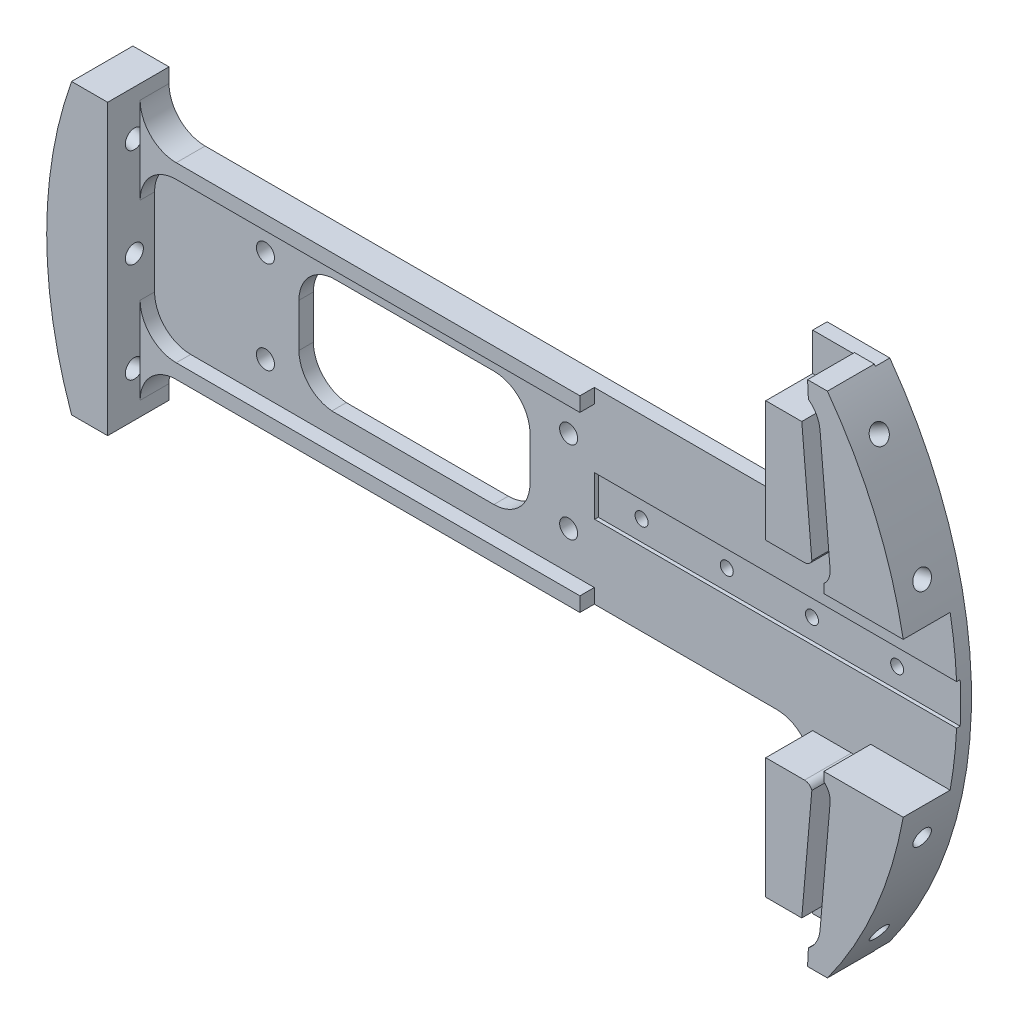
SolidWorks part; units mm, degrees
ref_plane "Front Plane" through (0, 0, 0) normal (0, 0, 1) x (1, 0, 0)
ref_plane "Top Plane" through (0, 0, 0) normal (0, 1, 0) x (1, 0, 0)
ref_plane "Right Plane" through (0, 0, 0) normal (1, 0, 0) x (0, 0, -1)
sketch "Sketch1" plane through (0, 0, 0) normal (0, 0, 1) x (1, 0, 0)
  line L0 (0, 0) -> (91.8237, 0) construction
  line L2 (-71.5726, 25.4) -> (-65.2226, 25.4)
  line L3 (50.546, 44.45) -> (50.546, 22.86)
  line L4 (50.546, -44.45) -> (50.546, -22.86)
  line L5 (44.196, -16.51) -> (-58.8726, -16.51)
  line L6 (50.546, 44.45) -> (61.5792, 44.45)
  line L7 (50.546, -44.45) -> (61.5792, -44.45)
  line L8 (-65.2226, -22.86) -> (-65.2226, -25.4)
  line L9 (44.196, 16.51) -> (-58.8726, 16.51)
  line L10 (-65.2226, 22.86) -> (-65.2226, 25.4)
  line L11 (-71.5726, -25.4) -> (-65.2226, -25.4)
  arc A0 (61.5792, -44.45) -> (61.5792, 44.45) centre (0, 0) ccw
  circle A1 centre (0, 0) radius 75.946 construction
  arc A2 (-71.5726, 25.4) -> (-71.5726, -25.4) centre (0, 0) ccw
  circle A3 centre (-45.72, 8.128) radius 1.5875
  circle A4 centre (-45.72, -8.128) radius 1.5875
  arc A5 (50.546, 22.86) -> (44.196, 16.51) centre (44.196, 22.86) cw
  arc A6 (-58.8726, 16.51) -> (-65.2226, 22.86) centre (-58.8726, 22.86) cw
  arc A7 (50.546, -22.86) -> (44.196, -16.51) centre (44.196, -22.86) ccw
  arc A8 (-58.8726, -16.51) -> (-65.2226, -22.86) centre (-58.8726, -22.86) ccw
  point P6 (75.946, 0)
  point P17 (0, 0)
  point P30 (50.546, -16.51)
  point P33 (-65.2226, -16.51)
  dimension "D1" = 75.946
  dimension "D8" = 151.892
  dimension "D11" = 75.946
  dimension "D13" = 6.35
  dimension "D7" = 3.175
  dimension ".125" = 3.175
  dimension "D2" = 27.94
  dimension "D3" = 6.35
  dimension "D4" = 11.0332
  dimension "D5" = 50.8
  dimension "D6" = 88.9
  dimension "D9" = 8.382
  dimension "D10" = 8.382
  dimension "D14" = 45.72
  dimension "1.8" = 45.72
extrude "Boss-Extrude1" add sketch "Sketch1" along normal blind 2.54
sketch "Sketch2" plane through (0, 0, 2.54) normal (0, 0, 1) x (1, 0, 0)
  line L0 (60.2463, 17.78) -> (56.2059, 64.1603) construction
  line L1 (-13.9228, 0) -> (116.9939, 0) construction
  line L2 (35.7924, 17.78) -> (109.7023, 17.78) construction
  line L3 (61.8653, 17.78) -> (60.0951, 38.1)
  line L4 (58.6516, 17.5) -> (56.8815, 37.82)
  line L5 (56.8815, 37.82) -> (50.546, 37.82)
  line L6 (58.0471, 41.7789) -> (57.9008, 44.704)
  line L7 (57.9008, 44.704) -> (61.395, 44.704)
  line L8 (50.546, 37.82) -> (50.546, 16.5667)
  line L9 (50.546, 16.5667) -> (57.3661, 16.5667)
  line L10 (60.7595, 15.0941) -> (60.7595, 13.5449)
  line L11 (60.7595, 13.5449) -> (74.7284, 13.5449)
  line L12 (60.2463, -17.78) -> (56.2059, -64.1603) construction
  line L13 (60.7595, -13.5449) -> (74.7284, -13.5449)
  line L14 (60.7595, -15.0941) -> (60.7595, -13.5449)
  line L15 (50.546, -16.5667) -> (57.3661, -16.5667)
  line L16 (50.546, -37.82) -> (50.546, -16.5667)
  line L17 (57.9008, -44.704) -> (61.395, -44.704)
  line L18 (58.0471, -41.7789) -> (57.9008, -44.704)
  line L19 (56.8815, -37.82) -> (50.546, -37.82)
  line L20 (58.6516, -17.5) -> (56.8815, -37.82)
  line L21 (61.8653, -17.78) -> (60.0951, -38.1)
  line L22 (96.3863, 0) -> (96.3863, 82.276) construction
  arc A0 (61.5792, -44.45) -> (61.5792, 44.45) centre (0, 0) ccw construction
  arc A1 (60.0951, 38.1) -> (58.0471, 41.7789) centre (54.9639, 37.653) ccw
  arc A2 (57.3661, 16.5667) -> (58.6516, 17.5) centre (57.3661, 17.9187) ccw
  arc A3 (61.8653, 17.78) -> (60.7595, 15.0941) centre (58.7167, 17.5057) cw
  arc A4 (74.7284, 13.5449) -> (61.395, 44.704) centre (0, 0) ccw
  arc A5 (74.7284, -13.5449) -> (61.395, -44.704) centre (0, 0) cw
  arc A6 (61.8653, -17.78) -> (60.7595, -15.0941) centre (58.7167, -17.5057) ccw
  arc A7 (57.3661, -16.5667) -> (58.6516, -17.5) centre (57.3661, -17.9187) cw
  arc A8 (60.0951, -38.1) -> (58.0471, -41.7789) centre (54.9639, -37.653) cw
  point P0 (75.946, 0)
  point P1 (60.2463, 17.78)
  point P49 (96.3863, 44.704)
  dimension "D6" = 75.946
  dimension "D1" = 17.78
  dimension "D2" = 15.6997
  dimension "D3" = 85.021
  dimension "D4" = 1.6129
  dimension "D5" = 20.32
  dimension "D7" = 44.704
  dimension "D8" = 44.704
  dimension "D9" = 25.4
extrude "Boss-Extrude2" add sketch "Sketch2" along normal blind 8.255
sketch "Sketch3" plane through (0, 0, 2.54) normal (0, 0, 1) x (1, 0, 0)
  line L0 (-6.3906, 0) -> (92.2963, 0) construction
  line L1 (50.546, 44.45) -> (50.546, 22.86) construction
  line L2 (12.192, -3.55) -> (76.962, -3.55)
  line L3 (12.192, -3.55) -> (12.192, 3.55)
  line L4 (12.192, 3.55) -> (76.962, 3.55)
  line L5 (76.962, -3.55) -> (76.962, 3.55)
  line L6 (12.192, -3.55) -> (76.962, 3.55) construction
  line L7 (12.192, 3.55) -> (76.962, -3.55) construction
  point P3 (44.577, 0)
  dimension "D1" = 7.1
  dimension "D2" = 64.77
  dimension "D3" = 38.354
extrude "Cut-Extrude1" cut sketch "Sketch3" against normal blind 0.635
sketch "Sketch6" plane through (0, 0, 0) normal (0, 0, -1) x (-1, 0, 0)
  line L1 (102.4877, 0) -> (-122.8054, 0) construction
sketch "Sketch7" plane through (0, 0, 0) normal (0, 0, 1) x (1, 0, 0)
  line L0 (0, 0) -> (107.1474, 0) construction
  line L1 (0, 0) -> (65.9911, 38.1) construction
  dimension "D1" = 30
ref_plane "Plane2" through (65.7712, 37.973, 0) normal (0.866, 0.5, 0) x (0, 0, -1)
sketch "Sketch9" plane through (0, 0, 2.54) normal (0, 0, 1) x (1, 0, 0)
  line L0 (-35.0108, 0) -> (91.9546, 0) construction
  circle A0 centre (7.62, -7.239) radius 1.5875
  circle A1 centre (-45.72, 8.128) radius 1.5875 construction
  circle A4 centre (7.62, 7.239) radius 1.5875
  point P9 (74.93, 0)
  dimension "D6" = 3.175
  dimension "D1" = 53.34
  dimension "D4" = 74.93
  dimension "D7" = 7.239
extrude "Cut-Extrude4" cut sketch "Sketch9" against normal through all
sketch "Sketch4" plane through (0, 0, 1.905) normal (0, 0, 1) x (1, 0, 0)
  line L0 (12.192, 3.55) -> (12.192, -3.55) construction
  line L1 (-1.4827, 0) -> (103.4049, 0) construction
  circle A0 centre (19.812, 0) radius 1.143
  circle A1 centre (34.798, 0) radius 1.143
  circle A2 centre (49.784, 0) radius 1.143
  circle A3 centre (64.77, 0) radius 1.143
  point P2 (12.192, 0)
  dimension "D2" = 2.286
  dimension "D4" = 14.986
  dimension "D1" = 7.62
  dimension "D5" = 19.812
  dimension "D3" = 4
extrude "Cut-Extrude2" cut sketch "Sketch4" against normal blind 11.43
sketch "Sketch19" plane through (0, 0, 2.54) normal (0, 0, 1) x (1, 0, 0)
  line L0 (-71.5726, -25.4) -> (-65.2226, -25.4) construction
  line L3 (-71.5726, -25.4) -> (-65.2226, -25.4)
  line L4 (-65.2226, -25.4) -> (-65.2226, 25.4)
  line L5 (-65.2226, 25.4) -> (-71.5726, 25.4) construction
  line L6 (-65.2226, 25.4) -> (-71.5726, 25.4)
  circle A0 centre (0, 0) radius 75.946 construction
  arc A3 (-71.5726, 25.4) -> (-71.5726, -25.4) centre (0, 0) ccw
  point P0 (-65.2226, -25.4)
  point P6 (-71.5726, -25.4)
  dimension "D2" = 151.892
  dimension "D1" = 6.35
extrude "Boss-Extrude5" add sketch "Sketch19" along normal blind 8.255
ref_plane "Plane3" through (0, 0, 10.795) normal (0, 0, 1) x (1, 0, 0)
sketch "Sketch22" plane through (0, 0, 10.795) normal (0, 0, 1) x (1, 0, 0)
  line L1 (-75.946, -44.45) -> (75.946, -44.45) construction
  line L2 (-75.946, -44.45) -> (-75.946, 44.45) construction
  line L3 (-75.946, 44.45) -> (75.946, 44.45) construction
  line L4 (75.946, -44.45) -> (75.946, 44.45) construction
  line L5 (-75.946, -44.45) -> (75.946, 44.45) construction
  line L6 (-75.946, 44.45) -> (75.946, -44.45) construction
  point P0 (0, 0)
  dimension "D1" = 88.9
  dimension "D2" = 151.892
sketch "Sketch24" plane through (65.7712, 37.973, 0) normal (0.866, 0.5, 0) x (0, 0, -1)
  line L0 (0, -69.2844) -> (0, 7.7053) construction
  circle A0 centre (-6.0325, -2.2244) radius 1.6383
  dimension "D1" = 3.2766
  dimension "D2" = 6.0325
sketch "Sketch25" plane through (0, 0, 0) normal (0, 0, 1) x (1, 0, 0)
  line L0 (0, 0) -> (145.0129, 0) construction
  line L1 (0, 0) -> (140.0717, -37.5321) construction
  line L2 (0, 0) -> (125.5848, -72.5064) construction
  circle A0 centre (0, 0) radius 76.2 construction
  point P9 (0, 0)
  dimension "D1" = 152.4
  dimension "D2" = 3
ref_plane "Plane4" through (0, 0, 6.096) normal (0, 0, 1) x (1, 0, 0)
sketch "Sketch27" plane through (0, 0, 6.096) normal (0, 0, 1) x (1, 0, 0)
  line L0 (-98.5098, 0) -> (76.2, 0) construction
  line L1 (0, 0) -> (143.2275, -38.3777) construction
  line L2 (0, 0) -> (128.4143, -74.14) construction
  line L3 (0, 0) -> (143.2275, 38.3777) construction
  line L4 (0, 0) -> (128.4143, 74.14) construction
  line L5 (-95.1532, 25.4962) -> (73.6035, -19.722) construction
  line L6 (-95.1532, -25.4962) -> (73.6035, 19.722) construction
  circle A0 centre (0, 0) radius 76.2 construction
  point P5 (3.2671, -47.4697)
  point P10 (0, 0)
  point P13 (0, 0)
  point P17 (0, 0)
  point P19 (0, 0)
  dimension "D1" = 3
  dimension "D2" = 3
  dimension "D3" = 2
  dimension "D4" = 2
ref_plane "Plane5" through (65.7712, 37.973, 0) normal (0.866, 0.5, 0) x (0, 0, -1)
sketch "Sketch28" plane through (65.7712, 37.973, 0) normal (0.866, 0.5, 0) x (0, 0, -1)
  line L0 (0, -69.2844) -> (0, 7.7053) construction
  line L1 (-10.795, 8.0173) -> (-2.54, 8.0173) construction
  circle A0 centre (-6.0533, 0) radius 1.5875
  dimension "D1" = 3.175
  dimension "D2" = 6.0533
  dimension "D3" = 8.0173
extrude "Cut-Extrude12" cut sketch "Sketch28" against normal blind 7.62 contours A0
ref_plane "Plane6" through (73.3582, 19.6563, 0) normal (0.9659, 0.2588, 0) x (0, 0, -1)
ref_plane "Plane7" through (73.3582, -19.6563, 0) normal (0.9659, -0.2588, 0) x (0, 0, -1)
ref_plane "Plane8" through (65.7712, -37.973, 0) normal (0.866, -0.5, 0) x (0, 0, -1)
sketch "Sketch29" plane through (73.3582, 19.6563, 0) normal (0.9659, 0.2588, 0) x (0, 0, -1)
  circle A0 centre (-6.096, 0) radius 1.5875
  dimension "D1" = 3.175
extrude "Cut-Extrude13" cut sketch "Sketch29" against normal blind 10.16
ref_plane "Plane9" through (0, 0, 0) normal (0, 1, 0) x (1, 0, 0)
mirror "Mirror3" about plane through (0, 0, 0) normal (0, 1, 0) of "Cut-Extrude12", "Cut-Extrude13"
ref_plane "Plane10" through (-73.3582, 19.6563, 0) normal (-0.9659, 0.2588, 0) x (0, 0, 1)
ref_plane "Plane11" through (-75.946, 0, 0) normal (-1, 0, 0) x (0, 0, 1)
ref_plane "Plane12" through (-73.3582, -19.6563, 0) normal (-0.9659, -0.2588, 0) x (0, 0, 1)
sketch "Sketch30" plane through (-73.3582, 19.6563, 0) normal (-0.9659, 0.2588, 0) x (0, 0, 1)
  circle A0 centre (6.096, 0) radius 1.5875
  dimension "D1" = 3.175
extrude "Cut-Extrude14" cut sketch "Sketch30" against normal blind 12.7 contours A0
sketch "Sketch31" plane through (-75.946, 0, 0) normal (-1, 0, 0) x (0, 0, 1)
  circle A0 centre (6.096, 0) radius 1.5875
  dimension "D1" = 3.175
extrude "Cut-Extrude15" cut sketch "Sketch31" against normal blind 12.7
sketch "Sketch32" plane through (-73.3582, -19.6563, 0) normal (-0.9659, -0.2588, 0) x (0, 0, 1)
  circle A0 centre (6.096, 0) radius 1.5875
  dimension "D1" = 3.175
extrude "Cut-Extrude16" cut sketch "Sketch32" against normal blind 12.7
sketch "Sketch33" plane through (0, 0, 2.54) normal (0, 0, 1) x (1, 0, 0)
  line L0 (44.196, 16.51) -> (-58.8726, 16.51) construction
  line L1 (12.1373, 16.51) -> (-58.8726, 16.51)
  line L2 (44.196, 15.24) -> (-58.8726, 15.24) construction
  line L3 (12.1373, 13.97) -> (-58.8726, 13.97)
  line L4 (0, 0) -> (-34.589, 0) construction
  line L5 (-65.2226, 22.86) -> (-65.2226, 7.62)
  line L6 (12.1373, 13.97) -> (12.1373, 16.51)
  line L7 (12.1373, -13.97) -> (12.1373, -16.51)
  line L8 (44.196, 16.51) -> (-58.8726, 16.51) construction
  line L9 (44.196, -15.24) -> (-58.8726, -15.24) construction
  line L10 (12.1373, -16.51) -> (-58.8726, -16.51)
  line L11 (12.1373, -13.97) -> (-58.8726, -13.97)
  line L12 (-65.2226, -22.86) -> (-65.2226, -7.62)
  arc A0 (-65.2226, 22.86) -> (-58.8726, 16.51) centre (-58.8726, 22.86) ccw construction
  arc A1 (-65.2226, 22.86) -> (-58.8726, 16.51) centre (-58.8726, 22.86) ccw
  arc A2 (-65.2226, 7.62) -> (-58.8726, 13.97) centre (-58.8726, 7.62) cw
  arc A3 (-66.4926, 22.86) -> (-58.8726, 15.24) centre (-58.8726, 22.86) ccw construction
  arc A4 (-65.2226, -7.62) -> (-58.8726, -13.97) centre (-58.8726, -7.62) ccw
  arc A5 (-65.2226, -22.86) -> (-58.8726, -16.51) centre (-58.8726, -22.86) cw
  dimension "D2" = 71.0099
  dimension "D3" = 2.54
  dimension "D1" = 1.27
extrude "Boss-Extrude6" add sketch "Sketch33" along normal blind 2.54
sketch "Sketch34" plane through (0, 0, 2.54) normal (0, 0, 1) x (1, 0, 0)
  line L1 (-33.4726, 10.16) -> (-5.5326, 10.16)
  line L2 (-39.8226, -3.8353) -> (-39.8226, 3.81)
  line L3 (-5.5326, -10.16) -> (-34.0391, -10.16)
  line L4 (-58.8726, 13.97) -> (12.1373, 13.97) construction
  line L6 (-65.2226, -7.62) -> (-65.2226, 7.62) construction
  line L11 (0.8174, 3.81) -> (0.8174, -3.81)
  arc A2 (-34.0391, -10.16) -> (-39.8226, -3.8353) centre (-33.4726, -3.8353) cw
  arc A3 (-33.4726, 10.16) -> (-39.8226, 3.81) centre (-33.4726, 3.81) ccw
  arc A5 (0.8174, -3.81) -> (-5.5326, -10.16) centre (-5.5326, -3.81) cw
  arc A6 (0.8174, 3.81) -> (-5.5326, 10.16) centre (-5.5326, 3.81) ccw
  dimension "D3" = 6.35
  dimension "D8" = 7.62
  dimension "D6" = 6.35
  dimension "D7" = 7.6453
  dimension "D1" = 20.32
  dimension "D2" = 40.64
  dimension "D4" = 3.81
  dimension "D5" = 25.4
extrude "Cut-Extrude17" cut sketch "Sketch34" against normal through all
equation "\"0.15inin\"=0.2"
equation "\"0.45inin\"=0.35"
equation "\"0.55inin\"=0.45"
equation "\"0.125inin\"=0.325"
